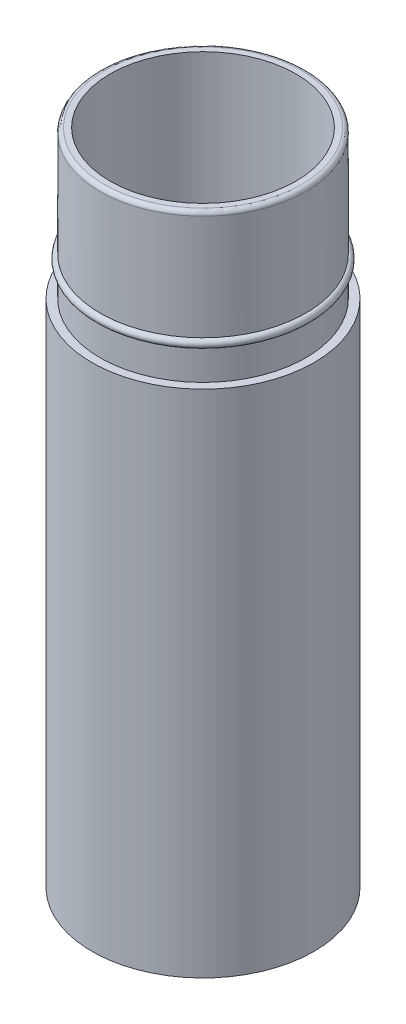
SolidWorks part; units mm, degrees
ref_plane "Front Plane" through (0, 0, 0) normal (0, 0, 1) x (1, 0, 0)
ref_plane "Top Plane" through (0, 0, 0) normal (0, 1, 0) x (1, 0, 0)
ref_plane "Right Plane" through (0, 0, 0) normal (1, 0, 0) x (0, 0, -1)
sketch "Sketch1" plane through (0, 0, 0) normal (0, 0, 1) x (1, 0, 0)
  line L0 (0, 52.2625) -> (0, -53.8034) construction
  line L1 (11.3, 0) -> (11.3, 80)
  line L2 (11.3, 80) -> (12.5, 80)
  line L3 (11.3, 0) -> (13.5, 0)
  line L4 (13.5, 0) -> (13.5, 62)
  line L5 (13.5, 62) -> (12.5, 62)
  line L6 (12.5, 62) -> (12.5, 65.7)
  line L7 (12.5, 66.7) -> (12.5, 80)
  arc A0 (12.5, 66.7) -> (12.5, 65.7) centre (12.5, 66.2) cw
  dimension "D5" = 0.5
  dimension "D1" = 22.6
  dimension "D2" = 27
  dimension "D3" = 25
  dimension "D4" = 62
  dimension "D6" = 4.2
  dimension "D7" = 80
revolve "Revolve1" add sketch "Sketch1" angle 360 about L0
fillet "Fillet1" radius 0.5 1 edges at (-12.5, 80, 0)
